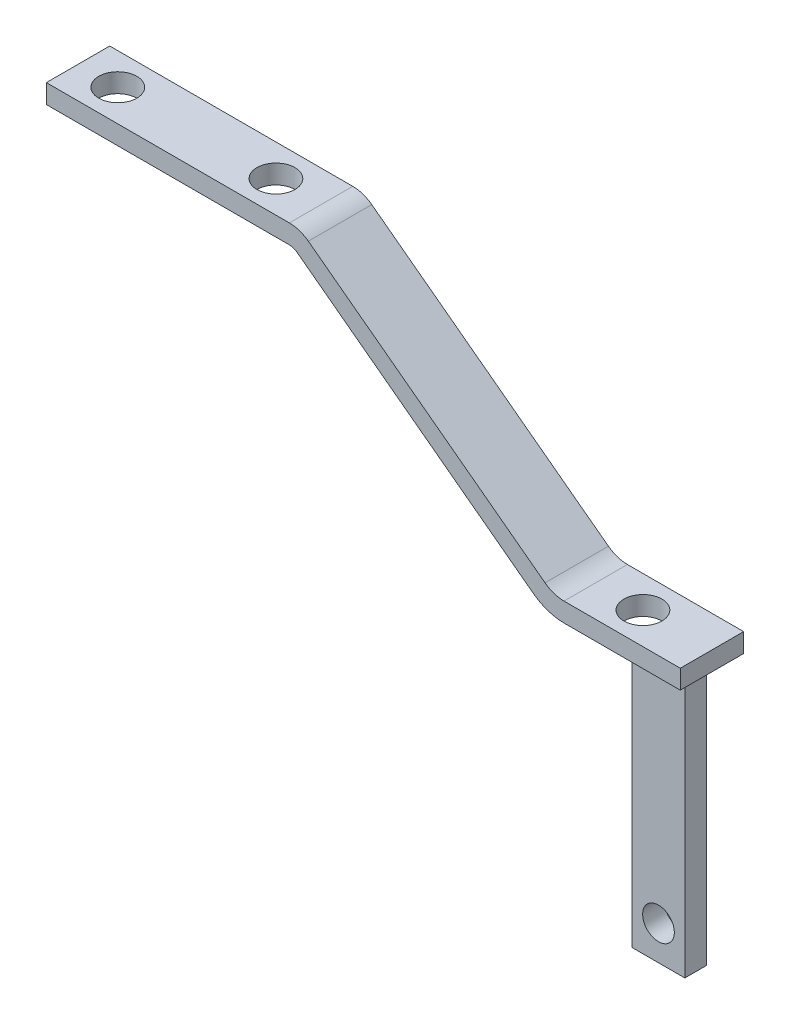
SolidWorks part; units mm, degrees
material "ABS"
ref_plane "Front Plane" through (0, 0, 0) normal (0, 0, 1) x (1, 0, 0)
ref_plane "Top Plane" through (0, 0, 0) normal (0, 1, 0) x (1, 0, 0)
ref_plane "Right Plane" through (0, 0, 0) normal (1, 0, 0) x (0, 0, -1)
sketch "Sketch1" plane through (0, 0, 0) normal (0, 0, 1) x (1, 0, 0)
  line L0 (0, 0) -> (100, 0) construction
  line L1 (100, 0) -> (100, -30) construction
  line L2 (0, 0) -> (38.3333, 0)
  line L3 (41.3333, -1) -> (78.6667, -29)
  line L4 (81.6667, -30) -> (100, -30)
  line L5 (0, -3) -> (38.3333, -3)
  line L6 (39.5333, -3.4) -> (76.8667, -31.4)
  line L7 (81.6667, -33) -> (100, -33)
  line L8 (100, -30) -> (100, -33)
  line L9 (0, 0) -> (0, -3)
  arc A0 (78.6667, -29) -> (81.6667, -30) centre (81.6667, -25) ccw
  arc A1 (38.3333, 0) -> (41.3333, -1) centre (38.3333, -5) cw
  arc A2 (38.3333, -3) -> (39.5333, -3.4) centre (38.3333, -5) cw
  arc A3 (76.8667, -31.4) -> (81.6667, -33) centre (81.6667, -25) ccw
  point P8 (80, -30)
  point P11 (40, 0)
  dimension "D4" = 5
  dimension "D1" = 100
  dimension "D2" = 20
  dimension "D3" = 40
  dimension "D5" = 3
extrude "Boss-Extrude1" add sketch "Sketch1" along normal blind 10
sketch "Sketch2" plane through (0, 0, 0) normal (0, 1, 0) x (1, 0, 0)
  line L0 (0, 0) -> (0, -10) construction
  line L1 (0, -5) -> (89.1114, -5) construction
  circle A0 centre (6.2676, -5) radius 3
  circle A1 centre (31.216, -5) radius 3
  circle A2 centre (89.1114, -5) radius 3
  point P6 (89.1114, -5)
  dimension "D1" = 6
  dimension "D2" = 6
  dimension "D3" = 6
extrude "Cut-Extrude1" cut sketch "Sketch2" against normal through all
sketch "Sketch3" plane through (0, -33, 0) normal (0, -1, 0) x (1, 0, 0)
  line L1 (91.3715, 5.5308) -> (99.6833, 5.5308)
  line L2 (91.3715, 5.5308) -> (91.3715, 8.9633)
  line L3 (91.3715, 8.9633) -> (99.6833, 8.9633)
  line L4 (99.6833, 5.5308) -> (99.6833, 8.9633)
  line L5 (91.3715, 5.5308) -> (99.6833, 8.9633) construction
  line L6 (91.3715, 8.9633) -> (99.6833, 5.5308) construction
  point P0 (95.5274, 7.2471)
  point P5 (95.5274, 7.2471)
extrude "Boss-Extrude2" add sketch "Sketch3" along normal blind 40
sketch "Sketch4" plane through (0, 0, 8.9633) normal (0, 0, 1) x (1, 0, 0)
  line L0 (95.5274, -73) -> (95.5274, -177.8853) construction
  line L1 (99.6833, -73) -> (91.3715, -73) construction
  circle A0 centre (95.5274, -67.6145) radius 2.5
  point P6 (105.6519, -77.1616)
  point P7 (95.5274, -67.6145)
  dimension "D1" = 5
extrude "Cut-Extrude2" cut sketch "Sketch4" against normal through all
